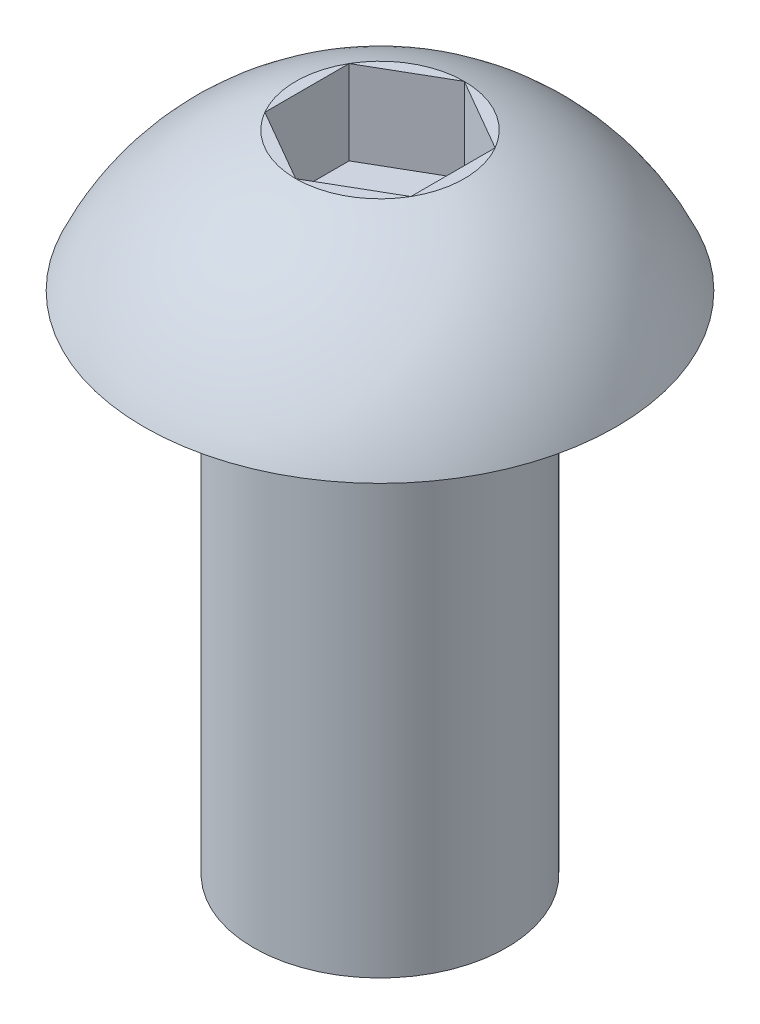
SolidWorks part; units mm, degrees
material "1023 Carbon Steel Sheet (SS)"
ref_plane "Front Plane" through (0, 0, 0) normal (0, 0, 1) x (1, 0, 0)
ref_plane "Top Plane" through (0, 0, 0) normal (0, 1, 0) x (1, 0, 0)
ref_plane "Right Plane" through (0, 0, 0) normal (1, 0, 0) x (0, 0, -1)
sketch "Sketch1" plane through (0, 0, 0) normal (1, 0, 0) x (0, 0, -1)
  line L2 (0, 0) -> (0, 1.65)
  line L3 (0, 1.65) -> (-1, 1.65)
  line L4 (0, 0) -> (-2.8, 0)
  line L5 (0, 4.7253) -> (0, -3.8299) construction
  arc A1 (-2.8, 0) -> (-1, 1.65) centre (-0.0483, -1.195) cw
  dimension "D2" = 1
  dimension "D4" = 1.65
  dimension "D3" = 3
  dimension "D1" = 2.8
revolve "Revolve1" add sketch "Sketch1" angle 360 about L5
sketch "Sketch2" plane through (0, 0, 0) normal (0, -1, 0) x (1, 0, 0)
  circle A0 centre (0, 0) radius 1.5
  dimension "D1" = 3
extrude "Boss-Extrude1" add sketch "Sketch2" along normal blind 6
sketch "Sketch3" plane through (0, 1.65, 0) normal (0, 1, 0) x (1, 0, 0)
  line L1 (0, 1) -> (-0.866, 0.5)
  line L2 (-0.866, 0.5) -> (-0.866, -0.5)
  line L3 (-0.866, -0.5) -> (0, -1)
  line L4 (0, -1) -> (0.866, -0.5)
  line L5 (0.866, -0.5) -> (0.866, 0.5)
  line L6 (0.866, 0.5) -> (0, 1)
  circle A0 centre (0, 0) radius 0.866 construction
  dimension "D1" = 1
extrude "Cut-Extrude1" cut sketch "Sketch3" against normal blind 1
